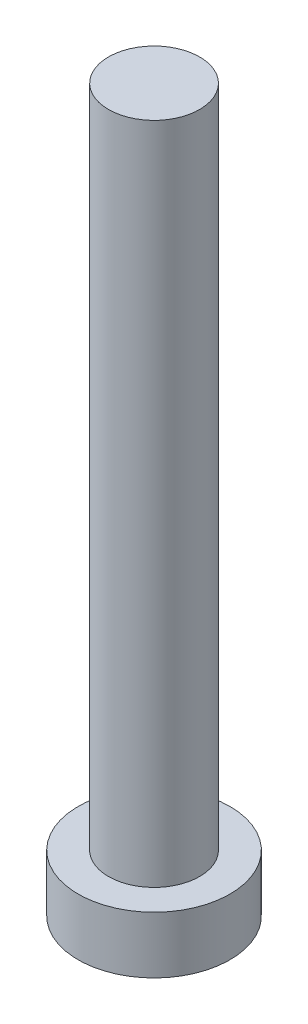
SolidWorks part; units mm, degrees
ref_plane "Front Plane" through (0, 0, 0) normal (0, 0, 1) x (1, 0, 0)
ref_plane "Top Plane" through (0, 0, 0) normal (0, 1, 0) x (1, 0, 0)
ref_plane "Right Plane" through (0, 0, 0) normal (1, 0, 0) x (0, 0, -1)
sketch "Sketch1" plane through (0, 0, 0) normal (0, 1, 0) x (1, 0, 0)
  circle A0 centre (0, 0) radius 3.048
  dimension "D1" = 6.096
extrude "Boss-Extrude1" add sketch "Sketch1" along normal blind 44.45
sketch "Sketch2" plane through (0, 0, 0) normal (0, -1, 0) x (1, 0, 0)
  circle A0 centre (0, 0) radius 5.08
  dimension "D1" = 10.16
extrude "Boss-Extrude2" add sketch "Sketch2" along normal blind 3.81 contours A0
